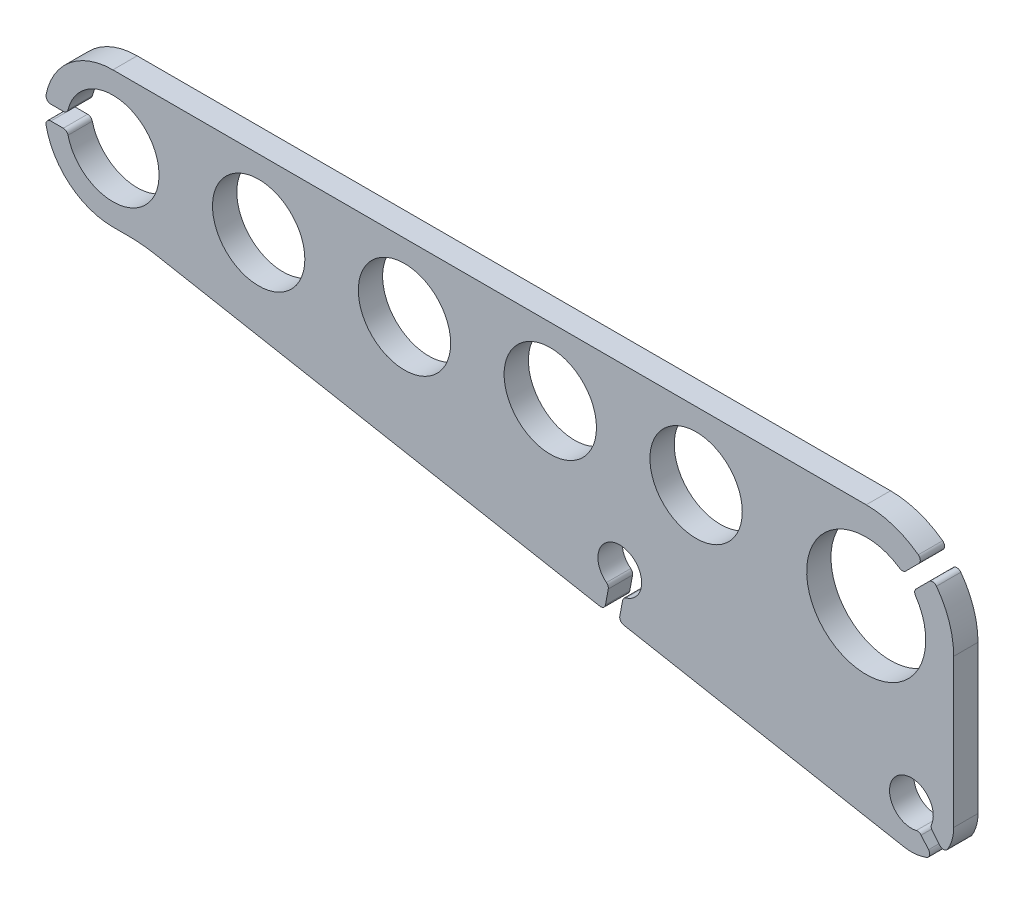
SolidWorks part; units mm, degrees
ref_plane "Plane1" through (0, 0, 0) normal (0, 0, 1) x (1, 0, 0)
ref_plane "Plane2" through (0, 0, 0) normal (0, 1, 0) x (1, 0, 0)
ref_plane "Plane3" through (0, 0, 0) normal (1, 0, 0) x (0, 0, -1)
sketch "Sketch1" plane through (0, 0, 0) normal (0, 0, 1) x (1, 0, 0)
  line L0 (90, 0) -> (120, 0) construction
  line L1 (0, 14) -> (155, 14)
  line L2 (173, -4) -> (173, -34.5)
  line L3 (162.7107, -43.0576) -> (105.1008, -32.3802)
  line L4 (104.2967, 0) -> (104.2967, -23) construction
  line L5 (0, -14) -> (3.1735, -14)
  line L6 (0, 0) -> (-18.4266, 0) construction
  line L7 (-12.7574, 1.5) -> (-10.198, 1.5)
  line L8 (-12.7574, -1.5) -> (-10.198, -1.5)
  line L9 (164.1614, -34.3387) -> (176.1538, -48.6307) construction
  line L10 (168.5948, -37.2887) -> (170.1293, -39.1175)
  line L11 (166.2966, -39.217) -> (167.8312, -41.0458)
  line L12 (155, -4) -> (183.3177, 24.3177) construction
  line L13 (165.2615, 4.1402) -> (167.9508, 6.8295)
  line L14 (163.1402, 6.2615) -> (165.8295, 8.9508)
  line L15 (104.2967, -23) -> (102.6426, -31.9246) construction
  line L16 (104.8788, -28.0903) -> (104.2997, -31.2147)
  line L17 (101.9291, -27.5436) -> (101.35, -30.668)
  line L18 (100.1845, -31.469) -> (8.6406, -14.5024)
  arc A0 (-9.2268, -2.2619) -> (-9.2268, 2.2619) centre (0, 0) ccw
  circle A1 centre (30, 0) radius 9.5
  circle A2 centre (60, 0) radius 9.5
  circle A3 centre (90, 0) radius 9.5
  circle A4 centre (120, 0) radius 9.5
  arc A5 (161.8721, 6.1408) -> (165.1408, 2.8721) centre (155, -4) ccw
  arc A6 (0, -14) -> (-13.7387, -2.6923) centre (0, 0) cw
  arc A7 (155, 14) -> (165.7178, 10.4613) centre (155, -4) cw
  arc A8 (105.5775, -27.3139) -> (101.5551, -26.5684) centre (104.2967, -23) ccw
  arc A9 (168.4401, -36.2557) -> (165.3063, -38.8853) centre (164.2967, -34.5) ccw
  arc A10 (173, -34.5) -> (171.752, -38.9907) centre (164.2967, -34.5) cw
  arc A11 (8.6406, -14.5024) -> (3.1735, -14) centre (3.1735, -44) ccw
  arc A12 (-13.7387, 2.6923) -> (0, 14) centre (0, 0) cw
  arc A13 (-12.7574, 1.5) -> (-13.7387, 2.6923) centre (-12.7574, 2.5) cw
  arc A14 (-12.7574, -1.5) -> (-13.7387, -2.6923) centre (-12.7574, -2.5) ccw
  arc A15 (-10.198, -1.5) -> (-9.2268, -2.2619) centre (-10.198, -2.5) cw
  arc A16 (-10.198, 1.5) -> (-9.2268, 2.2619) centre (-10.198, 2.5) ccw
  arc A17 (167.4245, -42.6218) -> (162.7107, -43.0576) centre (164.2967, -34.5) cw
  arc A18 (170.1293, -39.1175) -> (171.752, -38.9907) centre (170.8954, -38.4747) ccw
  arc A19 (167.8312, -41.0458) -> (167.4245, -42.6218) centre (167.0652, -41.6886) cw
  arc A20 (166.2966, -39.217) -> (165.3063, -38.8853) centre (165.5306, -39.8598) ccw
  arc A21 (168.5948, -37.2887) -> (168.4401, -36.2557) centre (169.3608, -36.6459) cw
  arc A22 (169.4613, 6.7178) -> (173, -4) centre (155, -4) cw
  arc A23 (167.9508, 6.8295) -> (169.4613, 6.7178) centre (168.6579, 6.1224) cw
  arc A24 (165.8295, 8.9508) -> (165.7178, 10.4613) centre (165.1224, 9.6579) ccw
  arc A25 (163.1402, 6.2615) -> (161.8721, 6.1408) centre (162.4331, 6.9687) cw
  arc A26 (165.2615, 4.1402) -> (165.1408, 2.8721) centre (165.9687, 3.4331) ccw
  arc A27 (101.35, -30.668) -> (100.1845, -31.469) centre (100.3667, -30.4858) cw
  arc A28 (104.2997, -31.2147) -> (105.1008, -32.3802) centre (105.283, -31.3969) ccw
  arc A29 (104.8788, -28.0903) -> (105.5775, -27.3139) centre (105.8621, -28.2725) cw
  arc A30 (101.9291, -27.5436) -> (101.5551, -26.5684) centre (100.9458, -27.3614) ccw
  point P27 (173, -44.9646)
  point P37 (-13.9194, 1.5)
  point P40 (-13.9194, -1.5)
  point P43 (-9.3808, -1.5)
  point P46 (-9.3808, 1.5)
  point P54 (170.9564, -40.1032)
  point P57 (168.6583, -42.0315)
  point P60 (165.8748, -38.7142)
  point P63 (168.1729, -36.7859)
  point P70 (168.7443, 7.623)
  point P73 (166.623, 9.7443)
  point P76 (162.5362, 5.6575)
  point P79 (164.6575, 3.5362)
  point P86 (101.1677, -31.6513)
  point P89 (104.1175, -32.198)
  point P92 (104.9984, -27.445)
  point P95 (102.0487, -26.8982)
  dimension "D8" = 19
  dimension "D11" = 24.5
  dimension "D12" = 14
  dimension "D17" = 60
  dimension "D15" = 18
  dimension "D10" = 9
  dimension "D6" = 8.7033
  dimension "D14" = 30
  dimension "D20" = 1
  dimension "D23" = 1
  dimension "D26" = 1
  dimension "D28" = 1
  dimension "D2" = 30
  dimension "D3" = 30
  dimension "D4" = 30
  dimension "D5" = 35
  dimension "D7" = 9.0766
  dimension "D9" = 30
  dimension "D13" = 10.5
  dimension "D16" = 23
  dimension "D18" = 11.5
  dimension "D19" = 3
  dimension "D21" = 40
  dimension "D22" = 3
  dimension "D24" = 45
  dimension "D25" = 3
  dimension "D27" = 3
extrude "Extrude1" add sketch "Sketch1" along normal blind 5
